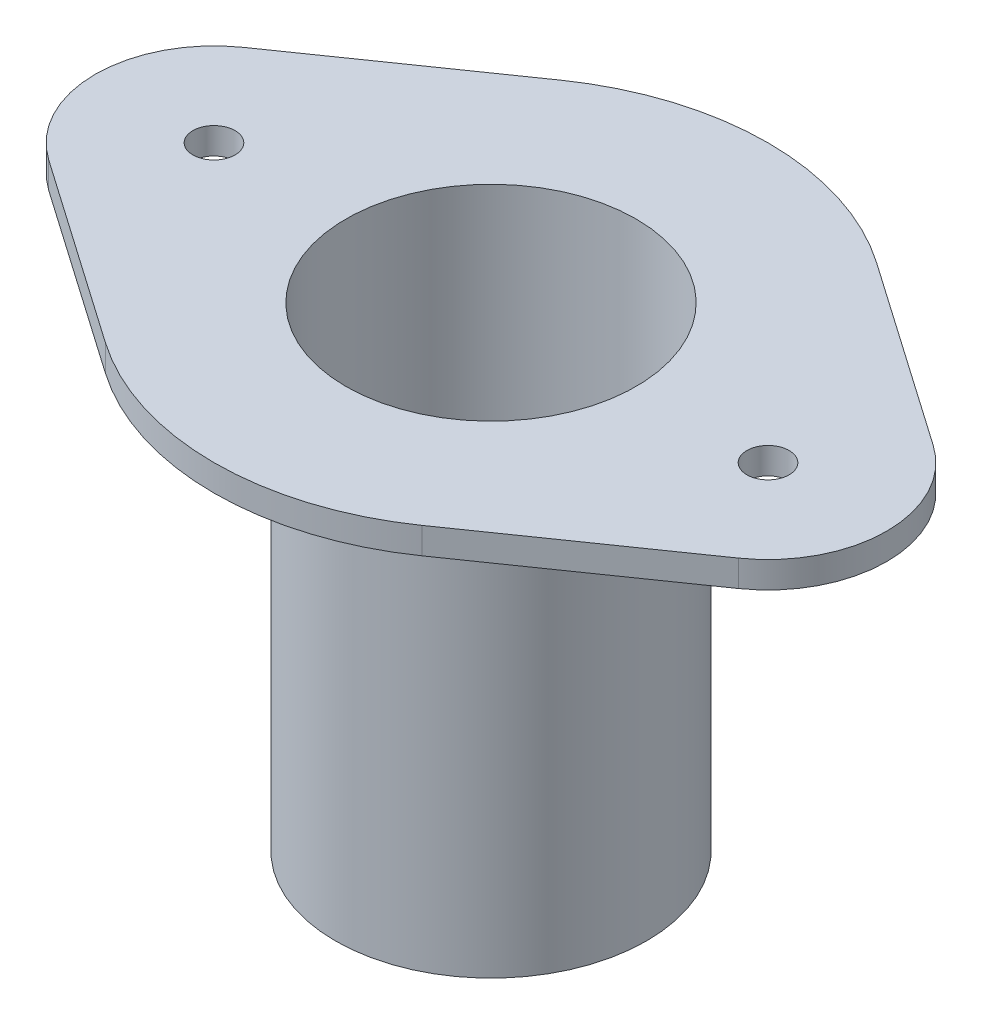
SolidWorks part; units mm, degrees
ref_plane "Front Plane" through (0, 0, 0) normal (0, 0, 1) x (1, 0, 0)
ref_plane "Top Plane" through (0, 0, 0) normal (0, 1, 0) x (1, 0, 0)
ref_plane "Right Plane" through (0, 0, 0) normal (1, 0, 0) x (0, 0, -1)
sketch "Sketch1" plane through (0, 0, 0) normal (0, 1, 0) x (1, 0, 0)
  circle A0 centre (0, 0) radius 29.5
  circle A1 centre (0, 0) radius 27.5
  dimension "D1" = 59
  dimension "D2" = 55
extrude "Boss-Extrude1" add sketch "Sketch1" along normal blind 85
sketch "Sketch2" plane through (0, 85, 0) normal (0, 1, 0) x (1, 0, 0)
  line L0 (30, 43.0842) -> (65.3571, 18.4647)
  line L1 (65.3571, -18.4647) -> (30, -43.0842)
  line L2 (-65.3571, -18.4647) -> (-30, -43.0842)
  line L3 (-65.3571, 18.4647) -> (-30, 43.0842)
  arc A0 (-30, -43.0842) -> (30, -43.0842) centre (0, 0) ccw
  arc A1 (65.3571, -18.4647) -> (65.3571, 18.4647) centre (52.5, 0) ccw
  arc A2 (-65.3571, 18.4647) -> (-65.3571, -18.4647) centre (-52.5, 0) ccw
  arc A3 (30, 43.0842) -> (-30, 43.0842) centre (0, 0) ccw
  circle A4 centre (52.5, 0) radius 4
  circle A5 centre (-52.5, 0) radius 4
  circle A6 centre (0, 0) radius 27.5 construction
  circle A7 centre (0, 0) radius 27.5
  dimension "D1" = 105
  dimension "D2" = 45
  dimension "D3" = 8
  dimension "D4" = 8
extrude "Boss-Extrude2" add sketch "Sketch2" along normal blind 5
